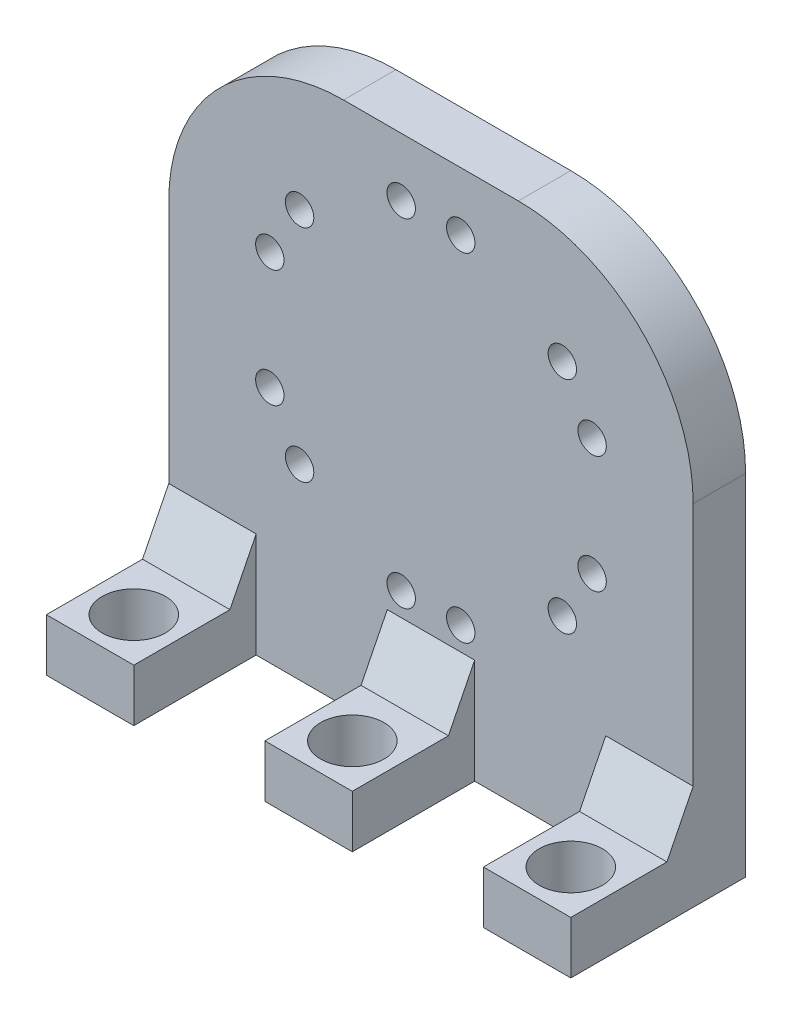
SolidWorks part; units mm, degrees
ref_plane "정면" through (0, 0, 0) normal (0, 0, 1) x (1, 0, 0)
ref_plane "윗면" through (0, 0, 0) normal (0, 1, 0) x (1, 0, 0)
ref_plane "우측면" through (0, 0, 0) normal (1, 0, 0) x (0, 0, -1)
sketch "Sketch1" plane through (0, 0, 0) normal (0, 0, 1) x (1, 0, 0)
  line L0 (30, 0) -> (0, 0) construction
  line L1 (-30, 30) -> (30, 30)
  line L2 (-30, 30) -> (-30, -30)
  line L3 (-30, -30) -> (30, -30)
  line L4 (30, 30) -> (30, -30)
  point P6 (0, 0)
  dimension "D1" = 60
  dimension "D2" = 60
  dimension "D3" = 30
extrude "Boss-Extrude1" add sketch "Sketch1" along normal blind 6
sketch "Sketch2" plane through (0, 0, 6) normal (0, 0, 1) x (1, 0, 0)
  line L0 (30, -30) -> (30, 30) construction
  line L1 (30, -24) -> (20, -24)
  line L2 (30, -24) -> (30, -30)
  line L3 (30, -30) -> (20, -30)
  line L4 (20, -24) -> (20, -30)
  line L5 (-30, -30) -> (30, -30) construction
  line L6 (0, 0) -> (0, -30) construction
  line L7 (0, -30) -> (25, -30) construction
  dimension "D1" = 25
  dimension "D2" = 10
  dimension "D3" = 6
extrude "Boss-Extrude2" add sketch "Sketch2" along normal blind 14 contours L1 L4 L3 L2
sketch "Sketch3" plane through (30, 0, 0) normal (1, 0, 0) x (0, 0, -1)
  line L0 (-6, -18) -> (-9, -24)
  line L1 (-6, -24) -> (-6, 30) construction
  line L2 (-20, -24) -> (-6, -24) construction
  line L3 (-9, -24) -> (-6, -24)
  line L4 (-6, -24) -> (-6, -18)
  dimension "D1" = 6
  dimension "D2" = 3
extrude "Boss-Extrude3" add sketch "Sketch3" against normal up to surface (10 mm away) up to face at (20, -27, 13)
sketch "Sketch4" plane through (0, -24, 0) normal (0, 1, 0) x (1, 0, 0)
  line L0 (25, -20) -> (25, 0) construction
  line L1 (30, -20) -> (20, -20) construction
  line L2 (30, 0) -> (-30, 0) construction
  circle A0 centre (25, -15) radius 3.625
  dimension "D1" = 7.25
  dimension "D2" = 5
extrude "Cut-Extrude1" cut sketch "Sketch4" against normal blind 15
pattern_linear "LPattern2" count 3 spacing 25 along (-1, 0, 0) of "Cut-Extrude1", "Boss-Extrude2", "Boss-Extrude3"
sketch "Sketch5" plane through (0, 0, 0) normal (0, 0, -1) x (-1, 0, 0)
  line L0 (0, 4) -> (0, 23.62) construction
  line L1 (0, 4) -> (3.407, 23.3219) construction
  line L2 (0, 4) -> (-3.407, 23.3219) construction
  line L3 (0, 4) -> (0, -30) construction
  line L4 (-5, -30) -> (5, -30) construction
  circle A0 centre (3.407, 23.3219) radius 1.625
  circle A1 centre (-3.407, 23.3219) radius 1.625
  dimension "D3" = 3.25
  dimension "D5" = 3.25
  dimension "D1" = 19.62
  dimension "D2" = 10
  dimension "D4" = 10
  dimension "D6" = 34
extrude "Cut-Extrude2" cut sketch "Sketch5" against normal blind 15
ref_plane "Plane1" through (0, 4, 0) normal (0, -1, 0) x (-1, 0, 0)
sketch "Sketch8" plane through (0, 4, 0) normal (0, -1, 0) x (-1, 0, 0)
  line L0 (0, 0) -> (0, -7.3713) construction
pattern_circular "CirPattern2" count 6 every 60 about axis through (0, 4, 0) along (0, 0, 1) of "Cut-Extrude2"
fillet "Fillet1" radius 20 2 edges at (-30, 30, 3) (30, 30, 3)
